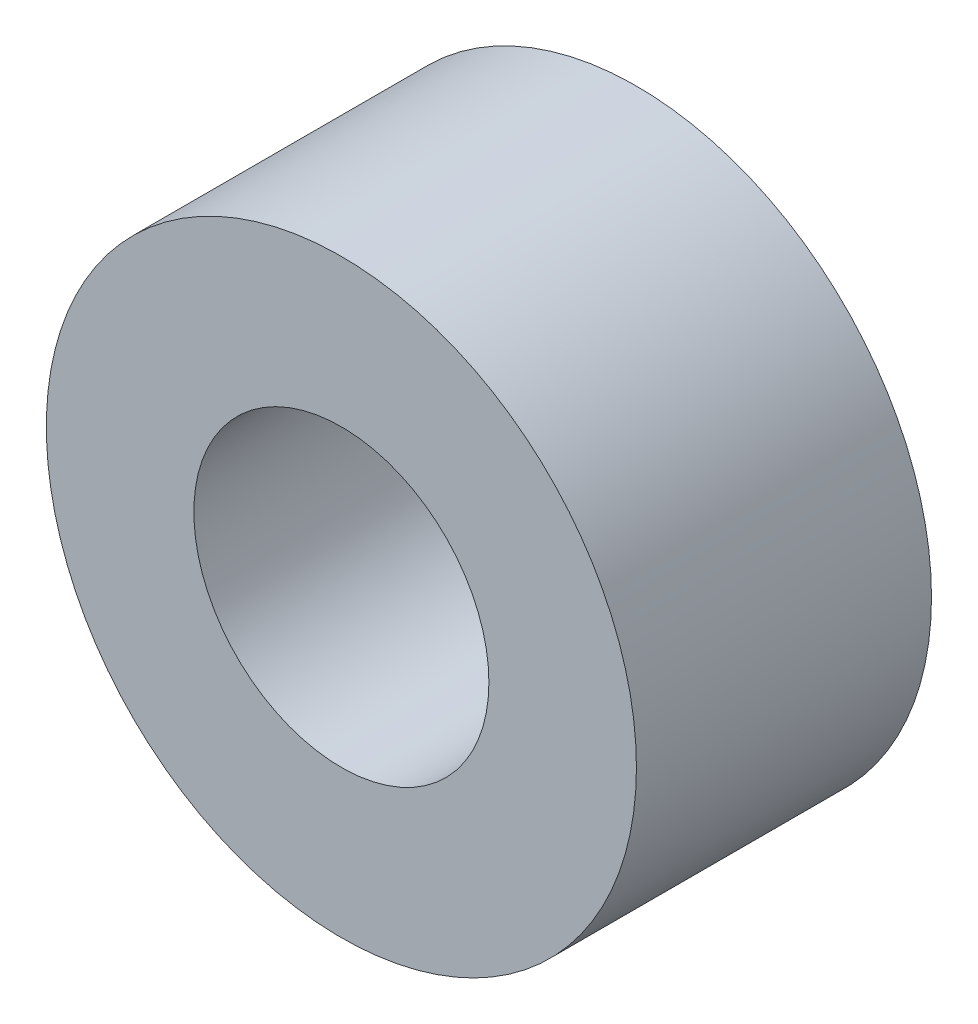
SolidWorks part; units mm, degrees
ref_plane "Front Plane" through (0, 0, 0) normal (0, 0, 1) x (1, 0, 0)
ref_plane "Top Plane" through (0, 0, 0) normal (0, 1, 0) x (1, 0, 0)
ref_plane "Right Plane" through (0, 0, 0) normal (1, 0, 0) x (0, 0, -1)
sketch "Sketch1" plane through (0, 0, 0) normal (0, 0, 1) x (1, 0, 0)
  circle A0 centre (-17.2958, 9.2291) radius 5
  circle A1 centre (-17.2958, 9.2291) radius 2.5
  dimension "D1" = 10
  dimension "D2" = 5
extrude "Boss-Extrude1" add sketch "Sketch1" along normal blind 5
